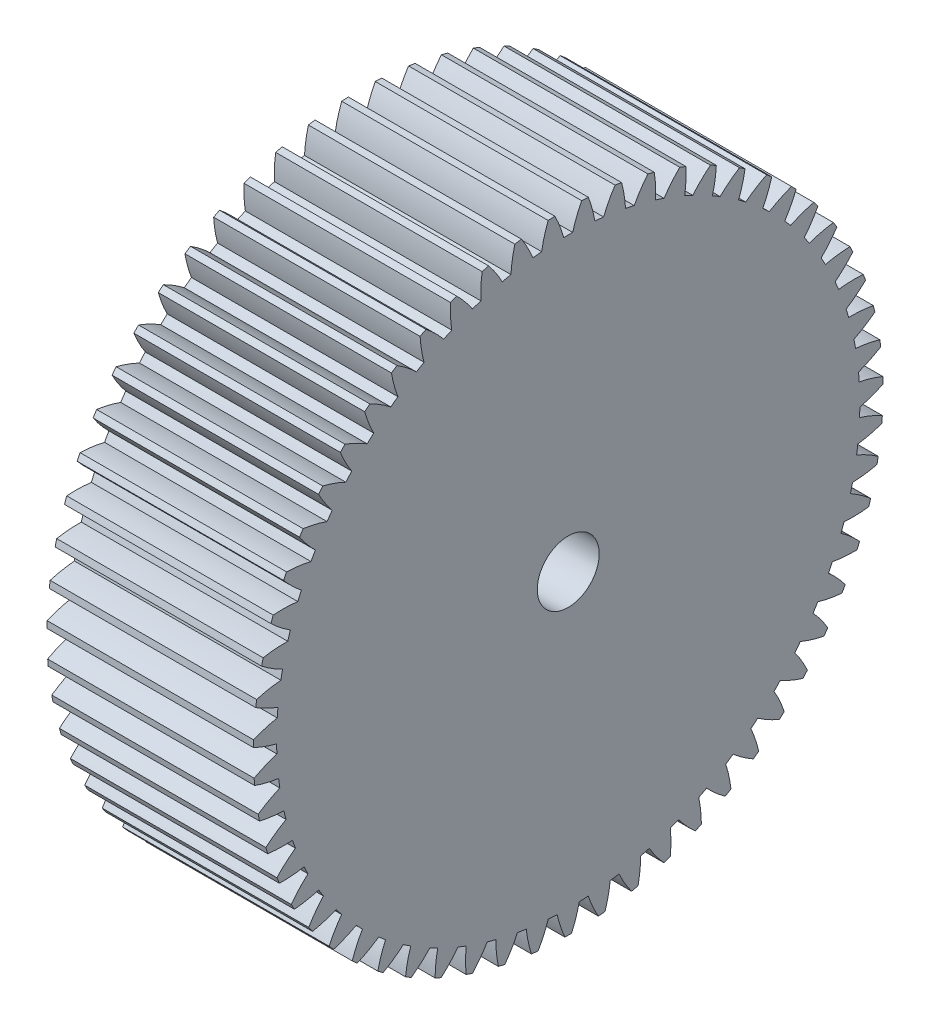
SolidWorks part; units mm, degrees
material "1.0035 (S185)"
ref_plane "Plane1" through (0, 0, 0) normal (0, 0, 1) x (1, 0, 0)
ref_plane "Plane2" through (0, 0, 0) normal (0, 1, 0) x (1, 0, 0)
ref_plane "Plane3" through (0, 0, 0) normal (1, 0, 0) x (0, 0, -1)
sketch "HoldingSke" plane through (0, 0, 0) normal (0, 1, 0) x (1, 0, 0)
  line L0 (0, 0) -> (1.0301, -1.7143)
  line L1 (-15, 0) -> (100, 0) construction
  line L2 (0, 0) -> (-2.1039, 2.3779)
  line L3 (0, 0) -> (-11.863, 4.5341)
  line L4 (0, 0) -> (4.4479, 7.4025)
  line L5 (0, 0) -> (-46.8476, -17.4728)
  line L6 (0, 0) -> (-8.2896, -5.593)
  line L7 (-2.1039, 2.3779) -> (8.6586, 51.2059)
  line L8 (-76.2, 54.61) -> (-75.7, 54.61)
  line L9 (-71.009, 38.7566) -> (-53.1078, 45.2721)
  line L10 (-76.2, 71.12) -> (104.1128, 71.12)
  line L11 (0, 0) -> (-10, 0)
  line L12 (-76.2, 101.6) -> (-76.181, 101.6)
  line L13 (24.9733, 27.94) -> (52.9518, 28.4284)
  line L14 (24.9733, 27.94) -> (24.9743, 27.94)
  line L15 (24.9733, 27.94) -> (100.4006, 29.5858)
  line L16 (-63.627, -0.5) -> (-12.827, -0.5)
  circle A0 centre (0, 0) radius 1.5
  circle A1 centre (0, 0) radius 14.124
  circle A2 centre (0, 0) radius 37.5
  circle A3 centre (0, 0) radius 1.5
  dimension "MHD" = 28.248
  dimension "Hub_dia" = 75
  dimension "Bore" = 3
  dimension "MBD" = 3
  dimension "Num_teeth" = 59
  dimension "Pitch_radius" = 180.3128
  dimension "Pitch" = 2
  dimension "Width" = 10
  dimension "Overall_len" = 50
  dimension "Show_teeth" = 59
  dimension "Thickness" = 10
  dimension "OAL" = 50.0001
  dimension "T_dim" = 0.5
  dimension "Ap" = 20
  dimension "H" = 19.05
  dimension "Backlash" = 0.019
  dimension "Addendum_fac" = 1
  dimension "Dedendum_fac" = 1.25
  dimension "Clearance_fac" = 0.25
  dimension "Dedendum_add" = 0.001
  dimension "Module" = 0.5
sketch "BasProSke" plane through (0, 0, 0) normal (0, 1, 0) x (1, 0, 0)
  line L0 (-10, 0) -> (60, 0) construction
  line L1 (0, 0) -> (0, 15.25)
  line L2 (0, 0) -> (10, 0)
  line L3 (10, 0) -> (10, 15.25)
  line L4 (10, 15.25) -> (0, 15.25)
  dimension "Diameter" = 30.5
  dimension "Thickness" = 10
revolve "Base-Revolve" add sketch "BasProSke" angle 360 about L0
sketch "TooCutSke" plane through (0, 0, 0) normal (1, 0, 0) x (0, 0, -1)
  line L1 (0, 0) -> (0, 107) construction
  line L2 (0, 0) -> (-0.4259, 14.7438) construction
  line L3 (0, 0) -> (-1.5696, 29.4494) construction
  line L4 (-0.4259, 14.7438) -> (-0.7848, 14.7247) construction
  arc A0 (0.2153, 14.1224) -> (-0.2153, 14.1224) centre (0, 0) ccw
  arc A1 (0.6635, 15.261) -> (-0.6635, 15.261) centre (0, 0) ccw
  circle A2 centre (0, 0) radius 14.75 construction
  circle A3 centre (0, 0) radius 13.8605 construction
  arc A4 (-0.2153, 14.1224) -> (-0.6635, 15.261) centre (-5.8997, 12.5422) ccw
  arc A5 (0.6635, 15.261) -> (0.2153, 14.1224) centre (5.8997, 12.5422) ccw
  dimension "Root_dia" = 28.248
  dimension "Overcut_dia" = 30.5508
  dimension "Pitch_dia" = 29.5
  dimension "Base_dia" = 27.7209
  dimension "Flank_rad" = 5.9
  dimension "Half_ang" = 3.051
  dimension "Half_CT" = 0.3594
extrude "ToothCut" cut sketch "TooCutSke" along normal through all
fillet "Breaks" [suppressed] radius 0.01
fillet "RootFillets" [suppressed] radius 0.126
pattern_circular "TeethCuts" count 59 every 6.102 about axis through (-10, 0, 0) along (1, 0, 0) of "ToothCut", "RootFillets", "Breaks"
sketch "HubNeaOneSke" plane through (0, 0, 0) normal (-1, 0, 0) x (0, 0, 1)
  circle A0 centre (0, 0) radius 14.124
  dimension "Diameter" = 28.248
extrude "HubNearOne" [suppressed] add sketch "HubNeaOneSke" along normal blind 40.0001
sketch "HubNeaBotSke" plane through (0, 0, 0) normal (-1, 0, 0) x (0, 0, 1)
  circle A0 centre (0, 0) radius 14.124
  dimension "Diameter" = 28.248
extrude "HubNearBoth" [suppressed] add sketch "HubNeaBotSke" along normal blind 20
ref_plane "FarPln" through (10, 0, 0) normal (1, 0, 0) x (0, 0, -1)
sketch "HubFarSke" plane through (10, 0, 0) normal (1, 0, 0) x (0, 0, -1)
  circle A0 centre (0, 0) radius 14.124
  dimension "Diameter" = 28.248
extrude "HubFar" [suppressed] add sketch "HubFarSke" along normal blind 20
sketch "BorSke" plane through (0, 0, 0) normal (1, 0, 0) x (0, 0, -1)
  circle A0 centre (0, 0) radius 1.5
  dimension "Diameter" = 3
extrude "Bore" cut sketch "BorSke" along normal mid plane 100.0001
sketch "KeySke" plane through (0, 0, 0) normal (1, 0, 0) x (0, 0, -1)
  line L0 (-0.6, 0) -> (-0.6, 2)
  line L1 (-0.6, 2) -> (0.6, 2)
  line L2 (0.6, 2) -> (0.6, 0)
  line L3 (0, 0) -> (0, 34) construction
  line L4 (-0.6, 0) -> (0.6, 0)
  dimension "Offset" = 2
  dimension "Width" = 1.2
extrude "Keyway" [suppressed] cut sketch "KeySke" along normal mid plane 100.0001
pattern_circular "Keyway2" [suppressed] count 2 every 90 about axis through (-10, 0, 0) along (1, 0, 0)
equation "' \"Module@HoldingSke\" = 6.35"
equation "' \"Num_teeth@HoldingSke\" = 12"
equation "' \"Ap@HoldingSke\" =  20"
equation "' \"Width@HoldingSke\" = 0.5 * 25.4"
equation "' \"Hub_dia@HoldingSke\"= 1 * 25.4"
equation "' \"Overall_len@HoldingSke\" = 1.0 * 25.4"
equation "' \"Bore@HoldingSke\" = 0.75 * 25.4"
equation "' \"T_dim@HoldingSke\" = 0.1 * 25.4"
equation "' \"Width@KeySke\" = 0.25 * 25.4"
equation "' \"Show_teeth@HoldingSke\" = 13"
equation "' \"Backlash@HoldingSke\" = 0.009 * 25.4"
equation "' \"Addendum_fac@HoldingSke\" = 1.0"
equation "' \"Dedendum_fac@HoldingSke\" = 1.25"
equation "' \"Dedendum_add@HoldingSke\" = 0.00005 * 25.4"
equation "' \"Clearance_fac@HoldingSke\" = 0.25"
equation "\"Pitch@HoldingSke\" = 1 / \"Module@HoldingSke\""
equation "\"Overcut_dia@TooCutSke\" = (\"Num_teeth@HoldingSke\" + 2 * \"Addendum_fac@HoldingSke\") / \"Pitch@HoldingSke\" + 0.002 * 25.4"
equation "\"Pitch_dia@TooCutSke\" = \"Num_teeth@HoldingSke\" / \"Pitch@HoldingSke\""
equation "\"Base_dia@TooCutSke\" = \"Num_teeth@HoldingSke\" / \"Pitch@HoldingSke\" * cos((\"Ap@HoldingSke\"  * 3.14159265 / 180))"
equation "\"Root_dia@TooCutSke\" = (\"Num_teeth@HoldingSke\" + 2) / \"Pitch@HoldingSke\" - 2 * (\"Addendum_fac@HoldingSke\" + \"Dedendum_fac@HoldingSke\") / \"Pitch@HoldingSke\" - \"Dedendum_add@HoldingSke\" * 2"
equation "\"Half_ang@TooCutSke\" = 180 / \"Num_teeth@HoldingSke\""
equation "\"Half_CT@TooCutSke\" = \"Num_teeth@HoldingSke\" / \"Pitch@HoldingSke\" * sin((3.14159265 / 2 / \"Num_teeth@HoldingSke\")) / 2 - 7 * \"Backlash@HoldingSke\" / 4"
equation "\"Flank_rad@TooCutSke\" = \"Num_teeth@HoldingSke\" / \"Pitch@HoldingSke\" / 5"
equation "\"Radius@RootFillets\" = \"Clearance_fac@HoldingSke\" / \"Pitch@HoldingSke\" + \"Dedendum_add@HoldingSke\""
equation "\"Break_rad@Breaks\" = 0.02 / \"Pitch@HoldingSke\""
equation "\"Thickness@HoldingSke\" = \"Width@HoldingSke\""
equation "\"OAL@HoldingSke\" = \"Thickness@HoldingSke\""
equation "\"MHD@HoldingSke\" = (\"Num_teeth@HoldingSke\" + 2) / \"Pitch@HoldingSke\" - 2 * (\"Addendum_fac@HoldingSke\" + \"Dedendum_fac@HoldingSke\")  / \"Pitch@HoldingSke\" - \"Dedendum_add@HoldingSke\" * 2"
equation "\"MBD@HoldingSke\" = (\"Num_teeth@HoldingSke\" + 2) / \"Pitch@HoldingSke\" - 2 * (\"Addendum_fac@HoldingSke\" + \"Dedendum_fac@HoldingSke\")  / \"Pitch@HoldingSke\" - \"Dedendum_add@HoldingSke\" * 2 - 0.002 * 25.4"
equation "\"MHD@HoldingSke\" = ((sgn( \"MHD@HoldingSke\" - \"Hub_dia@HoldingSke\" )-1)*( \"MHD@HoldingSke\" - \"Hub_dia@HoldingSke\" ))/-2+ \"Hub_dia@HoldingSke\""
equation "\"MBD@HoldingSke\" = ((sgn( \"MBD@HoldingSke\" - \"Bore@HoldingSke\" )-1)*( \"MBD@HoldingSke\" - \"Bore@HoldingSke\" ))/-2+ \"Bore@HoldingSke\""
equation "\"OAL@HoldingSke\" = ((sgn( \"OAL@HoldingSke\" - \"Overall_len@HoldingSke\" )+1)*( \"OAL@HoldingSke\" - \"Overall_len@HoldingSke\" ))/2 + \"Overall_len@HoldingSke\" + 0.000002 * 25.4"
equation "\"Num_teeth@TeethCuts\" = int( \"Show_teeth@HoldingSke\" ) + 1"
equation "\"Num_teeth@TeethCuts\" = ((sgn( \"Num_teeth@TeethCuts\" - \"Num_teeth@HoldingSke\" )-1)*( \"Num_teeth@TeethCuts\" - \"Num_teeth@HoldingSke\" ))/-2+ \"Num_teeth@HoldingSke\""
equation "\"Num_teeth@TeethCuts\" = ((sgn( \"Num_teeth@TeethCuts\" - 2.0)+1)*( \"Num_teeth@TeethCuts\" - 2.0))/2 +2.0"
equation "\"Angle@TeethCuts\" = 360.0 / \"Num_teeth@HoldingSke\""
equation "\"Diameter@BasProSke\" = (\"Num_teeth@HoldingSke\" + 2 * \"Addendum_fac@HoldingSke\") / \"Pitch@HoldingSke\""
equation "\"Thickness@BasProSke\"  = \"Thickness@HoldingSke\""
equation "' \"Fillet_rad@BasProSke\" =  \"Thickness@HoldingSke\" * 0.05"
equation "\"MHD@HoldingSke\" = ((sgn( \"MHD@HoldingSke\" - \"Root_dia@TooCutSke\" )-1)*( \"MHD@HoldingSke\" - \"Root_dia@TooCutSke\" ))/-2+ \"Root_dia@TooCutSke\""
equation "\"Diameter@HubNeaOneSke\" = \"MHD@HoldingSke\""
equation "\"Length@HubNearOne\" = \"OAL@HoldingSke\" - \"Thickness@BasProSke\""
equation "\"Diameter@HubNeaBotSke\" = \"MHD@HoldingSke\""
equation "\"Length@HubNearBoth\" = ( \"OAL@HoldingSke\" - \"Thickness@BasProSke\" ) / 2.0"
equation "\"Thickness@FarPln\" = \"Thickness@BasProSke\""
equation "\"Diameter@HubFarSke\" = \"MHD@HoldingSke\""
equation "\"Length@HubFar\" = ( \"OAL@HoldingSke\" - \"Thickness@BasProSke\" ) / 2.0"
equation "\"Diameter@BorSke\" = \"MBD@HoldingSke\""
equation "\"D1@Bore\" = \"OAL@HoldingSke\" * 2.0"
equation "\"D1@Keyway\" = \"OAL@HoldingSke\" * 2.0"
equation "\"Offset@KeySke\" = \"T_dim@HoldingSke\" + \"MBD@HoldingSke\" / 2.0"
